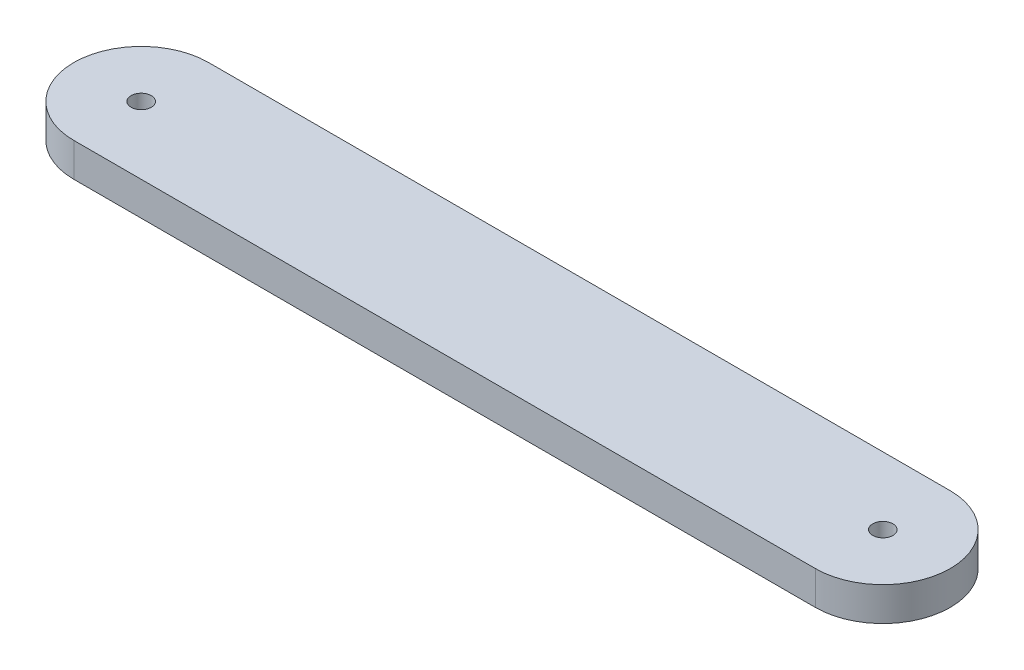
SolidWorks part; units mm, degrees
ref_plane "Front Plane" through (0, 0, 0) normal (0, 0, 1) x (1, 0, 0)
ref_plane "Top Plane" through (0, 0, 0) normal (0, 1, 0) x (1, 0, 0)
ref_plane "Right Plane" through (0, 0, 0) normal (1, 0, 0) x (0, 0, -1)
sketch "Sketch1" plane through (0, 0, 0) normal (0, 1, 0) x (1, 0, 0)
  line L0 (0, 0) -> (220, 0) construction
  line L1 (220, 20) -> (0, 20)
  line L6 (0, -20) -> (220, -20)
  arc A0 (0, 20) -> (0, -20) centre (0, 0) ccw
  arc A1 (220, -20) -> (220, 20) centre (220, 0) ccw
  circle A2 centre (0, 0) radius 3
  circle A3 centre (220, 0) radius 3
  dimension "D3" = 40
  dimension "D6" = 6
  dimension "D7" = 6
  dimension "D1" = 220
extrude "Boss-Extrude1" add sketch "Sketch1" along normal blind 10
